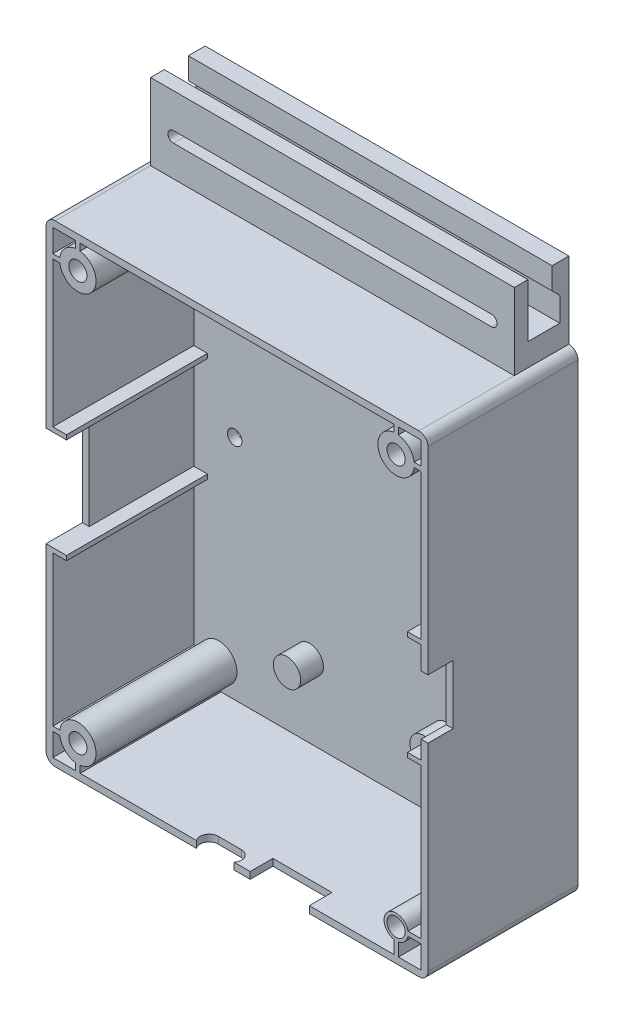
SolidWorks part; units mm, degrees
ref_plane "前视基准面" through (0, 0, 0) normal (0, 0, 1) x (1, 0, 0)
ref_plane "上视基准面" through (0, 0, 0) normal (0, 1, 0) x (1, 0, 0)
ref_plane "右视基准面" through (0, 0, 0) normal (1, 0, 0) x (0, 0, -1)
sketch "草图1" plane through (0, 0, 0) normal (0, 0, 1) x (1, 0, 0)
  line L0 (-1, 50) -> (-1, 40)
  line L1 (40, 50) -> (19, 50)
  line L2 (40, 50) -> (40, -50)
  line L3 (40, -50) -> (-40, -50)
  line L4 (-40, 50) -> (-40, -50)
  line L5 (40, 50) -> (-40, -50) construction
  line L6 (40, -50) -> (-40, 50) construction
  line L7 (-1, 40) -> (19, 40)
  line L8 (19, 40) -> (19, 50)
  line L9 (-1, 50) -> (-40, 50)
  circle A0 centre (-21.79, 39.3) radius 1.6
  circle A1 centre (21.79, 39.3) radius 1.6
  circle A2 centre (-21.79, -39.3) radius 1.6
  circle A3 centre (21.79, -39.3) radius 1.6
  circle A4 centre (-35, 45) radius 1.6
  circle A5 centre (35, 45) radius 1.6
  circle A6 centre (35, -45) radius 1.6
  circle A7 centre (-35, -45) radius 1.6
  point P0 (0, 0)
  dimension "D7" = 3.2
  dimension "D8" = 3.2
  dimension "D13" = 3.2
  dimension "D14" = 3.2
  dimension "D15" = 3.2
  dimension "D16" = 3.2
  dimension "D17" = 3.2
  dimension "D18" = 3.2
  dimension "D1" = 100
  dimension "D2" = 80
  dimension "D3" = 5
  dimension "D4" = 5
  dimension "D5" = 5
  dimension "D6" = 5
  dimension "D9" = 5
  dimension "D10" = 5
  dimension "D11" = 5
  dimension "D12" = 5
  dimension "D19" = 18.21
  dimension "D20" = 10.7
  dimension "D21" = 10.7
  dimension "D22" = 18.21
  dimension "D23" = 18.21
  dimension "D24" = 18.21
  dimension "D25" = 10.7
  dimension "D26" = 10.7
  dimension "D27" = 39
  dimension "D28" = 59
  dimension "D29" = 10
sketch "草图2" plane through (0, 0, 0) normal (0, 0, 1) x (1, 0, 0)
  line L1 (-38.9686, -45.5) -> (-40.9686, -45.5)
  line L3 (-38.9686, -44.5) -> (-40.9686, -44.5)
  line L4 (-40.9686, -45.5) -> (-40.9686, -44.5)
  line L6 (-35.5, -48.9686) -> (-35.5, -50.9686)
  line L7 (-35.5, -50.9686) -> (-34.5, -50.9686)
  line L8 (-34.5, -48.9686) -> (-34.5, -50.9686)
  line L11 (-35.5, 50.9686) -> (-34.5, 50.9686)
  line L18 (-40.9686, 44.5) -> (-40.9686, 45.5)
  line L19 (34.5, 50.9686) -> (35.5, 50.9686)
  line L24 (-38.9686, 44.5) -> (-40.9686, 44.5)
  line L27 (-38.9686, 45.5) -> (-40.9686, 45.5)
  line L28 (-35.5, 48.9686) -> (-35.5, 50.9686)
  line L29 (40.9686, 44.5) -> (40.9686, 45.5)
  line L31 (40.6024, -44.5) -> (40.6024, -45.5)
  line L32 (-34.5, 48.9686) -> (-34.5, 50.9686)
  line L36 (34.5, 48.9686) -> (34.5, 50.9686)
  line L38 (34.5, -50.6024) -> (35.5, -50.6024)
  line L39 (35.5, 48.9686) -> (35.5, 50.9686)
  line L40 (38.9686, 45.5) -> (40.9686, 45.5)
  line L43 (38.9686, 44.5) -> (40.9686, 44.5)
  line L48 (37.6024, -44.5) -> (40.6024, -44.5)
  line L51 (37.6024, -45.5) -> (40.6024, -45.5)
  line L52 (35.5, -47.6024) -> (35.5, -50.6024)
  line L55 (34.5, -47.6024) -> (34.5, -50.6024)
  circle A0 centre (-35, 45) radius 2
  circle A1 centre (35, 45) radius 2
  circle A2 centre (-35, -45) radius 2
  circle A3 centre (35, -45) radius 2
  arc A4 (34.5, 48.9686) -> (38.9686, 44.5) centre (35, 45) ccw
  arc A5 (-35.5, 48.9686) -> (-38.9686, 45.5) centre (-35, 45) ccw
  arc A6 (37.6024, -44.5) -> (34.5, -47.6024) centre (35, -45) ccw
  arc A7 (-38.9686, -45.5) -> (-35.5, -48.9686) centre (-35, -45) ccw
  arc A8 (-34.5, -48.9686) -> (-38.9686, -44.5) centre (-35, -45) ccw
  arc A9 (-38.9686, 44.5) -> (-34.5, 48.9686) centre (-35, 45) ccw
  arc A10 (38.9686, 45.5) -> (35.5, 48.9686) centre (35, 45) ccw
  arc A12 (35.5, -47.6024) -> (37.6024, -45.5) centre (35, -45) ccw
  dimension "D1" = 4
  dimension "D2" = 4
  dimension "D3" = 4
  dimension "D4" = 4
  dimension "D5" = 8
  dimension "D6" = 8
  dimension "D7" = 5.3
  dimension "D8" = 8
  dimension "D9" = 2
  dimension "D10" = 2
  dimension "D11" = 1
  dimension "D12" = 1
  dimension "D13" = 2
  dimension "D14" = 2
  dimension "D15" = 1
  dimension "D16" = 1
  dimension "D17" = 2
  dimension "D18" = 2
  dimension "D19" = 1
  dimension "D20" = 1
  dimension "D21" = 3
  dimension "D22" = 3
extrude "凸台-拉伸1" add sketch "草图2" against normal blind 31
sketch "草图3" plane through (0, 0, -31) normal (0, 0, -1) x (-1, 0, 0)
  line L0 (-40, 50) -> (-40, -50) construction
  line L1 (-40.5, 50.5) -> (40.5, 50.5)
  line L2 (-40.5, 50.5) -> (-40.5, -50.5)
  line L3 (-40.5, -50.5) -> (40.5, -50.5)
  line L4 (40.5, 50.5) -> (40.5, -50.5)
  line L5 (-40.5, 50.5) -> (40.5, -50.5) construction
  line L6 (-40.5, -50.5) -> (40.5, 50.5) construction
  line L7 (-40, 50) -> (-19, 50) construction
  line L9 (-40, -52) -> (40, -52)
  line L10 (-42, -50) -> (-42, 50)
  line L11 (-40, 52) -> (40, 52)
  line L12 (42, -50) -> (42, 50)
  line L13 (-42, -52) -> (42, 52) construction
  line L14 (-42, 52) -> (42, -52) construction
  arc A0 (-40, 52) -> (-42, 50) centre (-40, 50) ccw
  arc A2 (-42, -50) -> (-40, -52) centre (-40, -50) ccw
  arc A4 (42, 50) -> (40, 52) centre (40, 50) ccw
  arc A5 (40, -52) -> (42, -50) centre (40, -50) ccw
  point P0 (0, 0)
  point P10 (0, 0)
  dimension "D5" = 4
  dimension "D7" = 4
  dimension "D1" = 0.5
  dimension "D2" = 0.5
  dimension "D3" = 1.5
  dimension "D4" = 1.5
extrude "凸台-拉伸2" add sketch "草图3" against normal blind 31 separate body
sketch "草图4" plane through (0, 0, -31) normal (0, 0, -1) x (-1, 0, 0)
  line L4 (40, 52) -> (-40, 52)
  line L5 (-42, 50) -> (-42, -50)
  line L6 (-40, -52) -> (40, -52)
  line L7 (42, -50) -> (42, 50)
  line L8 (40, 52) -> (-40, 52)
  line L9 (-42, 50) -> (-42, -50)
  line L10 (-40, -52) -> (40, -52)
  line L11 (42, -50) -> (42, 50)
  arc A4 (42, 50) -> (40, 52) centre (40, 50) ccw
  arc A5 (-40, 52) -> (-42, 50) centre (-40, 50) ccw
  arc A6 (-42, -50) -> (-40, -52) centre (-40, -50) ccw
  arc A7 (40, -52) -> (42, -50) centre (40, -50) ccw
  arc A8 (42, 50) -> (40, 52) centre (40, 50) ccw
  arc A9 (-40, 52) -> (-42, 50) centre (-40, 50) ccw
  arc A10 (-42, -50) -> (-40, -52) centre (-40, -50) ccw
  arc A11 (40, -52) -> (42, -50) centre (40, -50) ccw
  dimension "D1" = 0
extrude "凸台-拉伸3" add sketch "草图4" along normal blind 2
sketch "草图5" plane through (-42, 0, 0) normal (-1, 0, 0) x (0, 0, 1)
  line L1 (0, 11.5) -> (-8, 11.5)
  line L2 (0, 11.5) -> (0, -10.5)
  line L3 (0, -10.5) -> (-8, -10.5)
  line L4 (-8, 11.5) -> (-8, -10.5)
  line L5 (-33, 50) -> (0, 50) construction
  line L6 (-33, -50) -> (0, -50) construction
  line L7 (0, -50) -> (0, 50) construction
  dimension "D1" = 38.5
  dimension "D2" = 39.5
  dimension "D3" = 8
extrude "切除-拉伸1" cut sketch "草图5" against normal up to next
sketch "草图6" plane through (42, 0, 0) normal (1, 0, 0) x (0, 0, -1)
  line L1 (0, 6.5) -> (5.5, 6.5)
  line L2 (0, 6.5) -> (0, -6.5)
  line L3 (0, -6.5) -> (5.5, -6.5)
  line L4 (5.5, 6.5) -> (5.5, -6.5)
  line L5 (33, 50) -> (0, 50) construction
  line L6 (33, -50) -> (0, -50) construction
  line L7 (0, 50) -> (0, -50) construction
  dimension "D1" = 43.5
  dimension "D2" = 43.5
  dimension "D3" = 5.5
extrude "切除-拉伸2" cut sketch "草图6" against normal up to next
sketch "草图7" plane through (0, -52, 0) normal (0, -1, 0) x (1, 0, 0)
  line L0 (-2.213, -1.2) -> (-7.313, -1.2) construction
  line L1 (-2.213, -3.2) -> (-7.313, -3.2)
  line L2 (-2.213, 0.8) -> (-7.313, 0.8)
  line L3 (-40, -33) -> (-40, 0) construction
  line L4 (40, 0) -> (-40, 0) construction
  line L6 (2.897, 0) -> (15.897, 0)
  line L7 (2.897, 0) -> (2.897, -5)
  line L8 (2.897, -5) -> (15.897, -5)
  line L9 (15.897, 0) -> (15.897, -5)
  line L10 (-40.5, 0) -> (-35.5, 0) construction
  arc A0 (-2.213, -3.2) -> (-2.213, 0.8) centre (-2.213, -1.2) ccw
  arc A1 (-7.313, 0.8) -> (-7.313, -3.2) centre (-7.313, -1.2) ccw
  point P2 (-4.763, -1.2)
  point P7 (-9.313, -1.2)
  dimension "D2" = 37.787
  dimension "D3" = 2
  dimension "D1" = 30.687
  dimension "D4" = 3.2
  dimension "D5" = 42.897
  dimension "D6" = 55.897
  dimension "D7" = 5
extrude "切除-拉伸3" cut sketch "草图7" against normal up to next
sketch "草图8" plane through (0, 0, -31) normal (0, 0, 1) x (1, 0, 0)
  line L1 (-8.913, -52) -> (-40, -52) construction
  line L2 (40, -52) -> (15.897, -52) construction
  circle A0 centre (-15, -34.5) radius 3
  circle A1 centre (15, -34.5) radius 3
  circle A2 centre (-10, 46) radius 3
  circle A3 centre (10, 46) radius 3
  circle A4 centre (-10, 30) radius 3
  circle A5 centre (10, 30) radius 3
  dimension "D3" = 6
  dimension "D4" = 6
  dimension "D7" = 6
  dimension "D8" = 6
  dimension "D9" = 6
  dimension "D10" = 6
  dimension "D2" = 17.5
  dimension "D5" = 30
  dimension "D6" = 15
  dimension "D11" = 10
  dimension "D12" = 20
  dimension "D13" = 16
  dimension "D14" = 30
  dimension "D15" = 17.5
extrude "凸台-拉伸4" add sketch "草图8" along normal blind 5
sketch "草图9" plane through (0, 0, -33) normal (0, 0, -1) x (-1, 0, 0)
  line L4 (40, 52) -> (-40, 52)
  line L5 (-42, 50) -> (-42, -50)
  line L6 (-40, -52) -> (40, -52)
  line L7 (42, -50) -> (42, 50)
  line L8 (40, 52) -> (-40, 52)
  line L9 (-42, 50) -> (-42, -50)
  line L10 (-40, -52) -> (40, -52)
  line L11 (42, -50) -> (42, 50)
  circle A0 centre (10, 46) radius 3 construction
  circle A1 centre (-10, 46) radius 3 construction
  arc A4 (42, 50) -> (40, 52) centre (40, 50) ccw
  arc A5 (-40, 52) -> (-42, 50) centre (-40, 50) ccw
  arc A6 (-42, -50) -> (-40, -52) centre (-40, -50) ccw
  arc A7 (40, -52) -> (42, -50) centre (40, -50) ccw
  arc A8 (42, 50) -> (40, 52) centre (40, 50) ccw
  arc A9 (-40, 52) -> (-42, 50) centre (-40, 50) ccw
  arc A10 (-42, -50) -> (-40, -52) centre (-40, -50) ccw
  arc A11 (40, -52) -> (42, -50) centre (40, -50) ccw
  circle A12 centre (-15, -34.5) radius 2
  circle A13 centre (15, -34.5) radius 2
  circle A14 centre (10, 30) radius 3 construction
  circle A15 centre (-10, 30) radius 3 construction
  circle A22 centre (-10, 46) radius 2
  circle A23 centre (10, 46) radius 2
  circle A24 centre (10, 30) radius 2
  circle A25 centre (-10, 30) radius 2
  dimension "D2" = 4
  dimension "D3" = 4
  dimension "D4" = 4
  dimension "D5" = 4
  dimension "D6" = 4
  dimension "D7" = 4
  dimension "D8" = 17.5
  dimension "D9" = 17.5
  dimension "D1" = 0
extrude "切除-拉伸4" cut sketch "草图9" against normal blind 5 contours A12 | A13 | A22 | A23 | A24 | A25
sketch "草图10" plane through (0, 52, 0) normal (0, 1, 0) x (1, 0, 0)
  line L0 (-40, 33) -> (-40, 0) construction
  line L1 (40, 33) -> (-40, 33)
  line L2 (40, 33) -> (40, 21)
  line L3 (40, 21) -> (-40, 21)
  line L4 (-40, 33) -> (-40, 21)
  dimension "D1" = 12
extrude "凸台-拉伸5" add sketch "草图10" along normal blind 5
sketch "草图11" plane through (-40, 0, 0) normal (-1, 0, 0) x (0, 0, 1)
  line L0 (-33, 57) -> (-33, 68.8)
  line L1 (-33, 68.8) -> (-29.3, 68.8)
  line L2 (-29.3, 68.8) -> (-29.3, 64)
  line L3 (-29.3, 64) -> (-31, 62.3)
  line L4 (-31, 62.3) -> (-31, 57)
  line L5 (-33, 57) -> (-21, 57) construction
  line L7 (-24, 57) -> (-24, 68.8)
  line L8 (-24, 68.8) -> (-21, 68.8)
  line L9 (-21, 68.8) -> (-21, 57)
  line L10 (-21, 57) -> (-24, 57)
  line L11 (-33, 57) -> (-31, 57)
  dimension "D1" = 7
  dimension "D2" = 2
  dimension "D3" = 5.3
  dimension "D4" = 1.7
  dimension "D5" = 1.7
  dimension "D6" = 4.8
  dimension "D7" = 11.8
  dimension "D8" = 11.8
extrude "凸台-拉伸6" add sketch "草图11" against normal up to surface (80 mm away) up to face at (40, 54.5, -27)
sketch "草图12" plane through (0, 0, -24) normal (0, 0, -1) x (-1, 0, 0)
  line L0 (-35, 60) -> (35, 60) construction
  line L1 (-35, 61.2) -> (35, 61.2)
  line L2 (-35, 58.8) -> (35, 58.8)
  line L3 (-40, 57) -> (40, 57) construction
  arc A0 (-35, 61.2) -> (-35, 58.8) centre (-35, 60) ccw
  arc A1 (35, 58.8) -> (35, 61.2) centre (35, 60) ccw
  point P2 (0, 60)
  dimension "D2" = 1.2
  dimension "D1" = 3
  dimension "D3" = 35
extrude "切除-拉伸5" cut sketch "草图12" against normal up to surface (3 mm away) up to face at (0, 60.4, -21)
sketch "草图13" plane through (0, 0, -31) normal (0, 0, 1) x (1, 0, 0)
  line L0 (-40.5, 50.5) -> (-35.5, 50.5) construction
  circle A0 centre (-31.5, -0.5) radius 1.6
  circle A1 centre (31.5, -0.5) radius 1.6
  dimension "D1" = 3.2
  dimension "D2" = 3.2
  dimension "D3" = 51
  dimension "D4" = 51
  dimension "D5" = 63
  dimension "D6" = 31.5
extrude "切除-拉伸6" cut sketch "草图13" against normal through all
sketch "草图14" plane through (-40.5, 0, 0) normal (1, 0, 0) x (0, 0, -1)
  line L1 (0, 11.5) -> (31, 11.5)
  line L2 (0, 11.5) -> (0, 12.5)
  line L3 (0, 12.5) -> (31, 12.5)
  line L4 (31, 11.5) -> (31, 12.5)
  line L5 (0, 50) -> (0, -50) construction
  line L6 (31, -50.5) -> (31, -45.5) construction
  line L7 (8, 11.5) -> (0, 11.5) construction
  line L8 (0, -10.5) -> (8, -10.5) construction
  line L9 (0, -10.5) -> (31, -10.5)
  line L10 (0, -10.5) -> (0, -11.5)
  line L11 (0, -11.5) -> (31, -11.5)
  line L12 (31, -10.5) -> (31, -11.5)
  line L13 (0, -50) -> (0, 50) construction
  dimension "D2" = 1
  dimension "D3" = 1
extrude "凸台-拉伸7" add sketch "草图14" along normal blind 3
sketch "草图15" plane through (40.5, 0, 0) normal (-1, 0, 0) x (0, 0, 1)
  line L1 (0, 11.5) -> (-31, 11.5)
  line L2 (0, 11.5) -> (0, 12.5)
  line L3 (0, 12.5) -> (-31, 12.5)
  line L4 (-31, 11.5) -> (-31, 12.5)
  line L5 (0, -10.5) -> (-31, -10.5)
  line L6 (0, -10.5) -> (0, -11.5)
  line L7 (0, -11.5) -> (-31, -11.5)
  line L8 (-31, -10.5) -> (-31, -11.5)
  line L9 (0, 11.5) -> (-8, 11.5) construction
  line L10 (-8, -10.5) -> (0, -10.5) construction
  line L11 (-31, 50.5) -> (-31, 45.5) construction
  line L12 (0, -50) -> (0, 50) construction
  line L13 (0, 50) -> (0, -50) construction
  dimension "D3" = 1
  dimension "D4" = 1
extrude "凸台-拉伸8" add sketch "草图15" along normal blind 3
